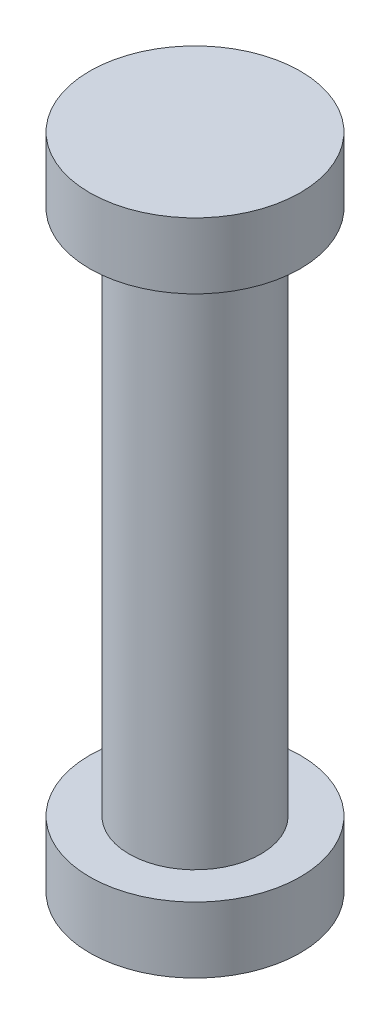
SolidWorks part; units mm, degrees
ref_plane "Płaszczyzna przednia" through (0, 0, 0) normal (0, 0, 1) x (1, 0, 0)
ref_plane "Płaszczyzna górna" through (0, 0, 0) normal (0, 1, 0) x (1, 0, 0)
ref_plane "Płaszczyzna prawa" through (0, 0, 0) normal (1, 0, 0) x (0, 0, -1)
sketch "Szkic1" plane through (0, 0, 0) normal (0, 1, 0) x (1, 0, 0)
  circle A0 centre (0, 0) radius 5
extrude "Dodanie-wyciągnięcie1" add sketch "Szkic1" along normal blind 40
sketch "Szkic2" plane through (0, 40, 0) normal (0, 1, 0) x (1, 0, 0)
  circle A0 centre (0, 0) radius 8
sketch "Szkic3" plane through (0, 0, 0) normal (0, -1, 0) x (1, 0, 0)
  circle A0 centre (0, 0) radius 8
extrude "Dodanie-wyciągnięcie2" add sketch "Szkic3" along normal blind 5
extrude "Dodanie-wyciągnięcie3" add sketch "Szkic2" along normal blind 5 contours A0
